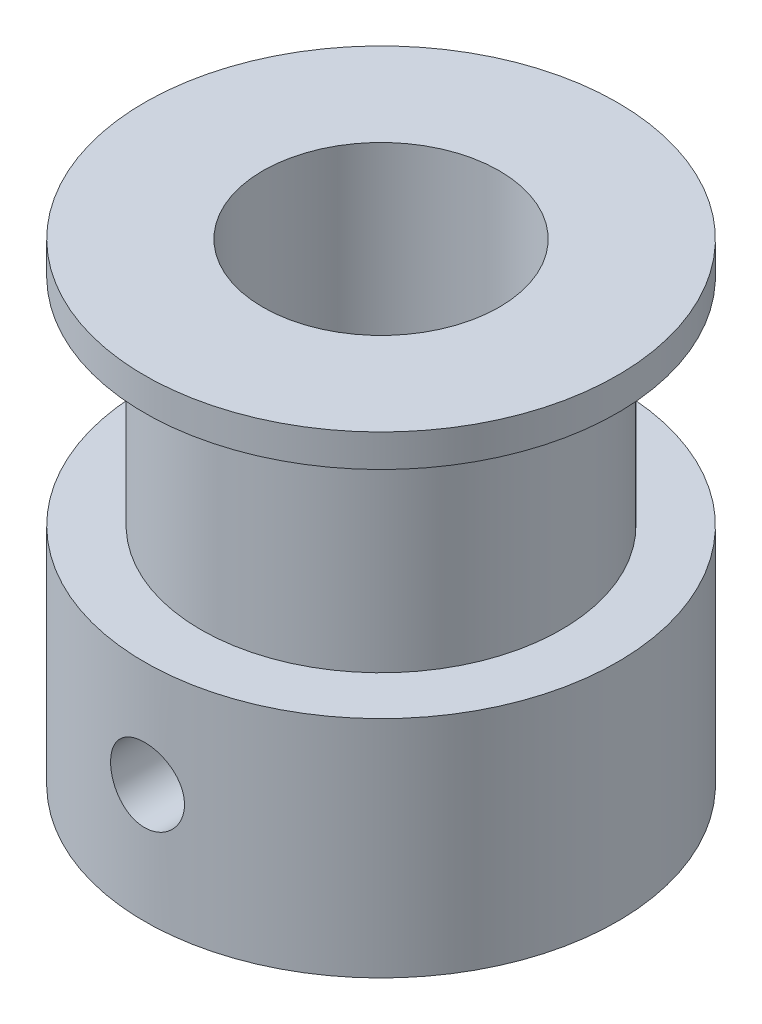
SolidWorks part; units mm, degrees
material "1060 Legierung"
ref_plane "Ebene vorne" through (0, 0, 0) normal (0, 0, 1) x (1, 0, 0)
ref_plane "Ebene oben" through (0, 0, 0) normal (0, 1, 0) x (1, 0, 0)
ref_plane "Ebene rechts" through (0, 0, 0) normal (1, 0, 0) x (0, 0, -1)
sketch "Skizze1" plane through (0, 0, 0) normal (0, 0, 1) x (1, 0, 0)
  line L0 (0, 0) -> (0, 18.9766) construction
  line L1 (-4, 16) -> (-4, 0)
  line L2 (-4, 0) -> (-8, 0)
  line L5 (-8, 0) -> (-8, 7.6)
  line L6 (-8, 7.6) -> (-6.1, 7.6)
  line L7 (-6.1, 7.6) -> (-6.1, 14.9)
  line L8 (-6.1, 14.9) -> (-8, 14.9)
  line L9 (-8, 14.9) -> (-8, 16)
  line L10 (-8, 16) -> (-4, 16)
  dimension "D1" = 8
  dimension "D2" = 1.1
  dimension "D3" = 12.2
  dimension "D4" = 16
  dimension "D6" = 7.3
  dimension "D7" = 16
revolve "Rotation1" add sketch "Skizze1" angle 360 about L0
ref_plane "Ebene1" through (0, 0, 8) normal (0, 0, 1) x (1, 0, 0)
hole_wizard "M3 Gewindebohrung1" positions "Skizze3" profile "Skizze4" tap size "M3" standard "ISO"
sketch "Skizze3" plane through (0, 0, 8) normal (0, 0, 1) x (1, 0, 0)
  line L0 (0, 4) -> (0, 0) construction
  point P0 (0, 4)
  dimension "D1" = 4
sketch "Skizze4" plane through (0, 4, 8) normal (1, 0, 0) x (0, -1, 0)
  line L0 (0, 0) -> (0, 4)
  line L1 (0, 4) -> (1.25, 4)
  line L2 (1.25, 4) -> (1.25, 0)
  line L5 (1.25, 0) -> (0, 0)
  line L11 (0, -6.35) -> (0, 107.95) construction
  dimension "Bohrerdurchmesser" = 2.5
  dimension "Bohrungstiefe" = 4
cosmetic thread "Bohrungsgewinde1"
pattern_circular "Kreismuster1" count 2 over 90 about axis through (0, 0, 0) along (0, -1, 0) of "M3 Gewindebohrung1"
cosmetic thread "Bohrungsgewinde2"
